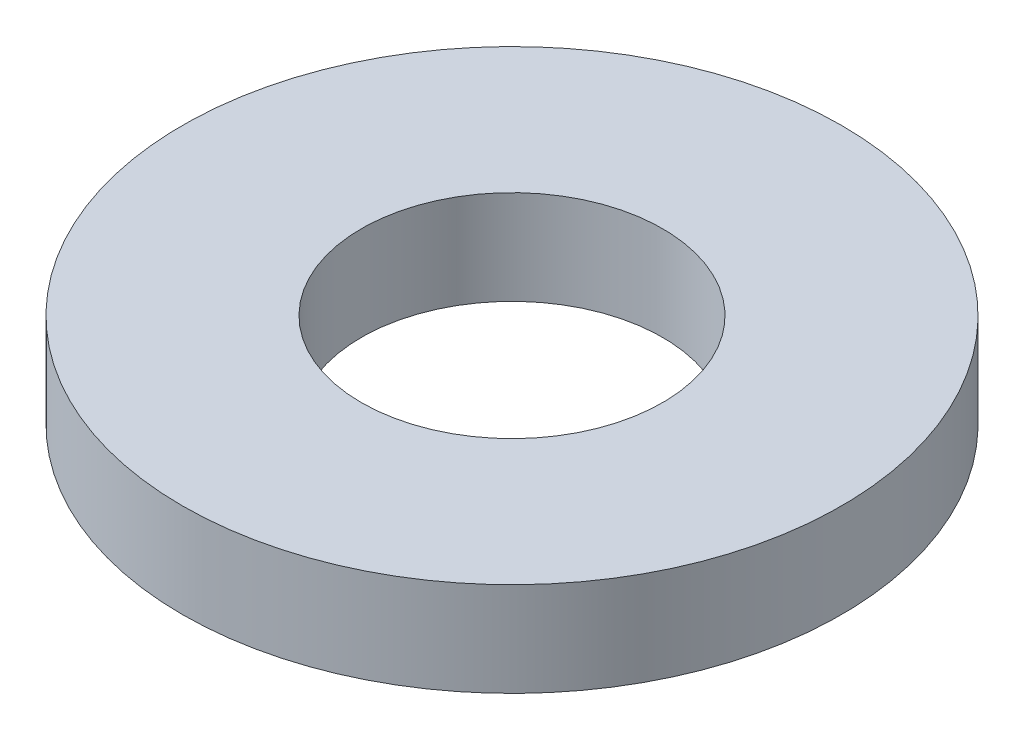
SolidWorks part; units mm, degrees
ref_plane "Alzado" through (0, 0, 0) normal (0, 0, 1) x (1, 0, 0)
ref_plane "Planta" through (0, 0, 0) normal (0, 1, 0) x (1, 0, 0)
ref_plane "Vista lateral" through (0, 0, 0) normal (1, 0, 0) x (0, 0, -1)
sketch "Sketch3" plane through (0, 0, 0) normal (0, 1, 0) x (1, 0, 0)
  circle A0 centre (0, 0) radius 1.6
  circle A1 centre (0, 0) radius 3.5
extrude "Boss-Extrude1" add sketch "Sketch3" along normal blind 1
